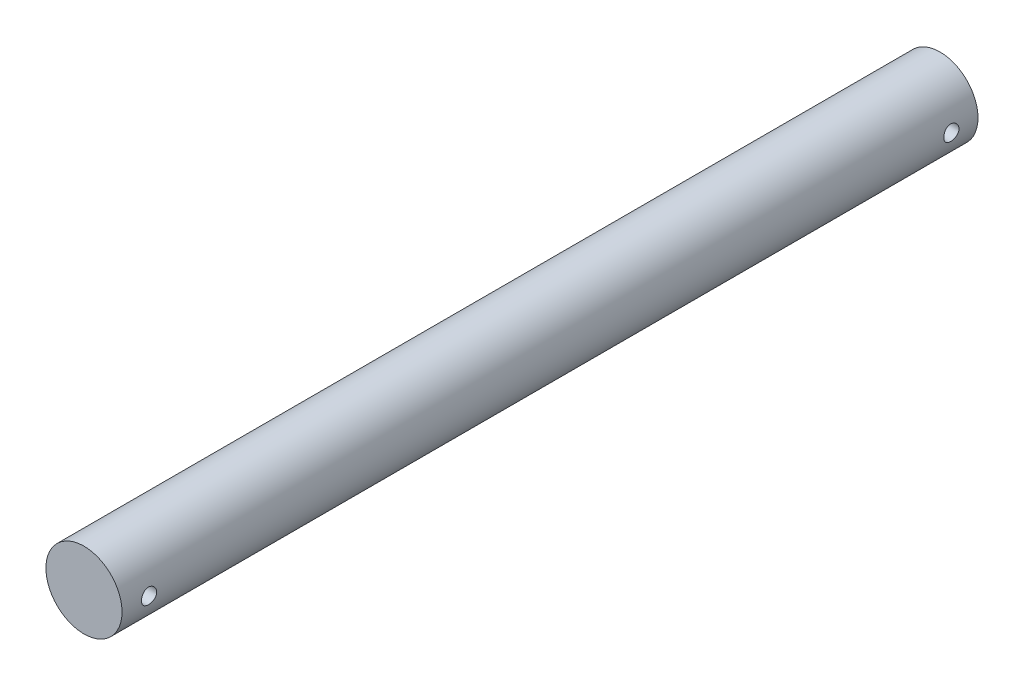
SolidWorks part; units mm, degrees
material "PVC Rigid"
ref_plane "Front Plane" through (0, 0, 0) normal (0, 0, 1) x (1, 0, 0)
ref_plane "Top Plane" through (0, 0, 0) normal (0, 1, 0) x (1, 0, 0)
ref_plane "Right Plane" through (0, 0, 0) normal (1, 0, 0) x (0, 0, -1)
sketch "Sketch1" plane through (0, 0, 0) normal (0, 0, 1) x (1, 0, 0)
  circle A0 centre (0, 0) radius 20
  dimension "D1" = 40
extrude "Boss-Extrude1" add sketch "Sketch1" along normal blind 450
sketch "Sketch2" plane through (0, 0, 0) normal (1, 0, 0) x (0, 0, -1)
  line L0 (-450, -20) -> (0, -20) construction
  line L2 (0, -20) -> (0, 20) construction
  circle A0 centre (-435.75, 0) radius 4
  circle A1 centre (-14, 0) radius 4
  point P7 (0, 0)
  dimension "D1" = 8
  dimension "D2" = 8
  dimension "D6" = 14
  dimension "D3" = 0
  dimension "D4" = 421.75
  dimension "D5" = 20
extrude "Cut-Extrude1" cut sketch "Sketch2" against normal through all both and the other way through all
